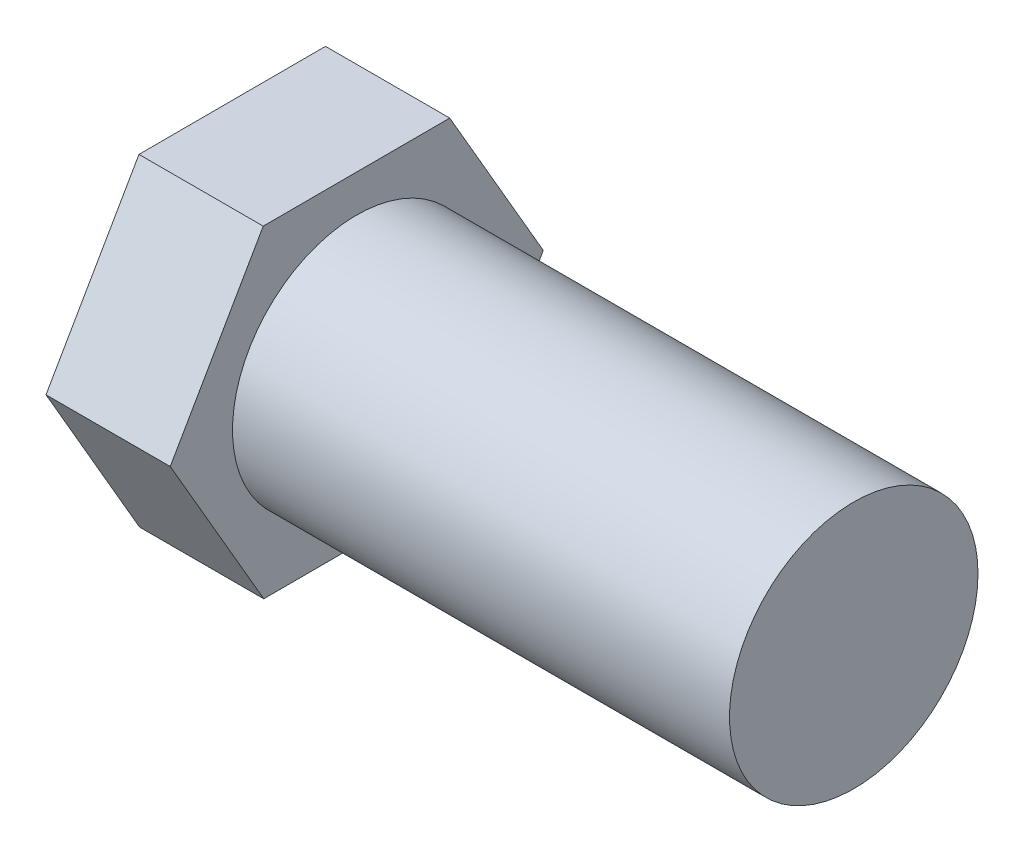
SolidWorks part; units mm, degrees
ref_plane "前视基准面" through (0, 0, 0) normal (0, 0, 1) x (1, 0, 0)
ref_plane "上视基准面" through (0, 0, 0) normal (0, 1, 0) x (1, 0, 0)
ref_plane "右视基准面" through (0, 0, 0) normal (1, 0, 0) x (0, 0, -1)
sketch "草图1" plane through (0, 0, 0) normal (1, 0, 0) x (0, 0, -1)
  line L1 (3.7643, -6.4934) -> (7.5055, 0.0133)
  line L2 (7.5055, 0.0133) -> (3.7413, 6.5066)
  line L3 (3.7413, 6.5066) -> (-3.7643, 6.4934)
  line L4 (-3.7643, 6.4934) -> (-7.5055, -0.0133)
  line L5 (-7.5055, -0.0133) -> (-3.7413, -6.5066)
  line L6 (-3.7413, -6.5066) -> (3.7643, -6.4934)
  circle A0 centre (0, 0) radius 6.5 construction
extrude "凸台-拉伸1" add sketch "草图1" along normal blind 5
sketch "草图2" plane through (5, 0, 0) normal (1, 0, 0) x (0, 0, -1)
  circle A0 centre (0, 0) radius 5
extrude "凸台-拉伸2" add sketch "草图2" along normal blind 20
